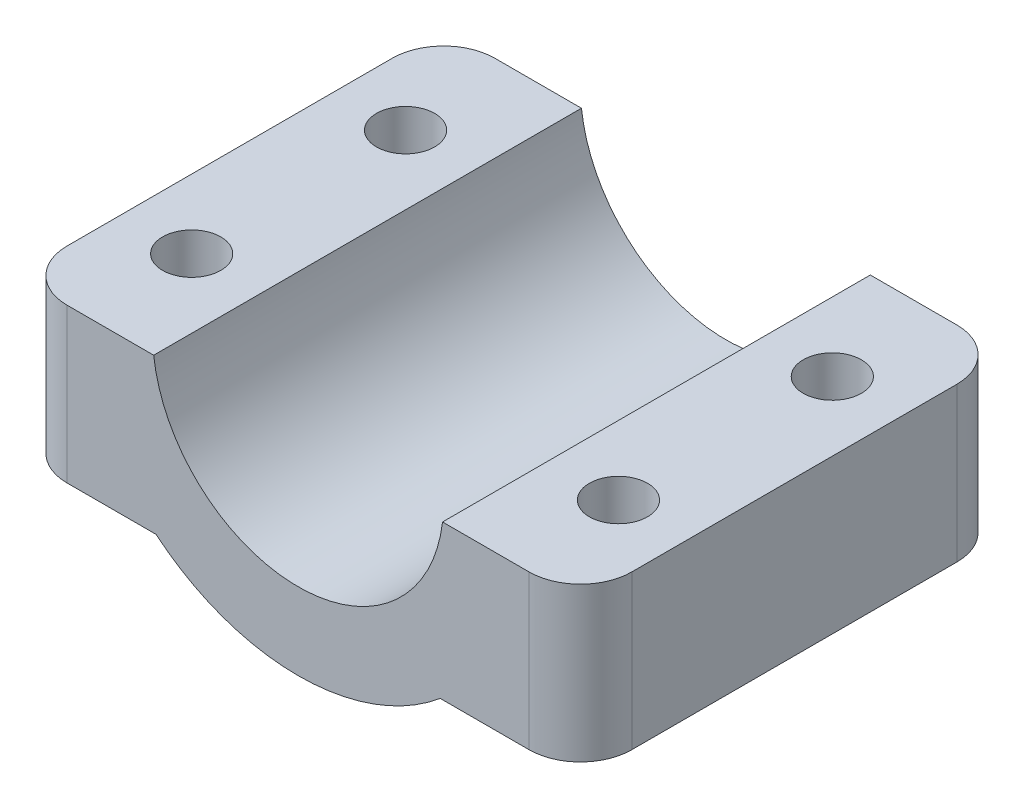
SolidWorks part; units mm, degrees
ref_plane "Alzado" through (0, 0, 0) normal (0, 0, 1) x (1, 0, 0)
ref_plane "Planta" through (0, 0, 0) normal (0, 1, 0) x (1, 0, 0)
ref_plane "Vista lateral" through (0, 0, 0) normal (1, 0, 0) x (0, 0, -1)
sketch "Croquis1" plane through (0, 0, 0) normal (0, 0, 1) x (1, 0, 0)
  line L0 (0, 0) -> (-17.9748, 0) construction
  line L1 (-16.5, 7.5) -> (-8.441, 7.5)
  line L2 (-16.5, 7.5) -> (-16.5, -1.5)
  line L5 (-16.5, 7.5) -> (16.5, -1.5) construction
  line L6 (-16.5, -1.5) -> (16.5, 7.5) construction
  line L15 (-16.5, -1.5) -> (-8.3066, -1.5)
  line L17 (8.441, 7.5) -> (16.5, 7.5)
  line L18 (8.3066, -1.5) -> (16.5, -1.5)
  line L19 (-12.4705, 7.5) -> (-12.4705, -1.5) construction
  line L20 (-14.1705, 7.5) -> (-14.1705, -1.5) construction
  line L21 (-10.7705, 7.5) -> (-10.7705, -1.5) construction
  line L22 (16.5, -1.5) -> (16.5, 7.5)
  arc A1 (-8.441, 7.5) -> (8.441, 7.5) centre (0, 8.5) ccw
  arc A7 (-8.3066, -1.5) -> (8.3066, -1.5) centre (0, 8.5) ccw
  point P0 (0, 0)
  point P7 (0, 0)
  dimension "D5" = 1
  dimension "D7" = 17
  dimension "D2" = 13
  dimension "D6" = 33
  dimension "D8" = 10
  dimension "D9" = 1.7
  dimension "D10" = 1.7
extrude "Saliente-Extruir1" add sketch "Croquis1" along normal mid plane 25
sketch "Croquis2" plane through (0, 7.5, 0) normal (0, 1, 0) x (1, 0, 0)
  line L0 (0, 12.5) -> (0, -12.5) construction
  line L1 (-8.441, -12.5) -> (8.441, -12.5) construction
  line L2 (8.441, 12.5) -> (-8.441, 12.5) construction
  line L3 (-16.5, 0) -> (16.5, 0) construction
  line L4 (-16.5, -12.5) -> (-16.5, 12.5) construction
  line L5 (16.5, -12.5) -> (16.5, 12.5) construction
  line L6 (-8.441, -12.5) -> (-16.5, -12.5) construction
  line L7 (-8.441, -12.5) -> (-16.5, -12.5) construction
  line L8 (-16.5, 0) -> (-16.5, 12.5) construction
  circle A2 centre (-12.4705, 6.25) radius 1.7
  circle A3 centre (12.4705, 6.25) radius 1.7
  circle A4 centre (12.4705, -6.25) radius 1.7
  circle A5 centre (-12.4705, -6.25) radius 1.7
  point P10 (-16.5, 6.25)
  point P13 (0, 12.5)
  point P24 (-12.4705, -12.5)
  dimension "D1" = 3.4
extrude "Cortar-Extruir1" cut sketch "Croquis2" against normal up to surface (9 mm away) contours A2
sketch "Croquis6" plane through (0, -1.5, 0) normal (0, -1, 0) x (1, 0, 0)
  line L0 (0, 6.25) -> (0, -6.25) construction
  line L1 (-12.4705, -6.25) -> (12.4705, -6.25) construction
  line L2 (-12.4705, -6.25) -> (-12.4705, 6.25) construction
  line L3 (-12.4705, 6.25) -> (12.4705, 6.25) construction
  line L4 (12.4705, -6.25) -> (12.4705, 6.25) construction
  line L5 (-12.4705, 0) -> (12.4705, 0) construction
  circle A0 centre (-12.4705, 6.25) radius 3.1
  circle A1 centre (12.4705, 6.25) radius 3.1
  circle A2 centre (12.4705, -6.25) radius 3.1
  circle A3 centre (-12.4705, -6.25) radius 3.1
  dimension "D1" = 6.2
extrude "Cortar-Extruir4" cut sketch "Croquis6" against normal blind 3
fillet "Redondeo1" radius 3 4 edges at (-16.5, 3, -12.5) (-16.5, 3, 12.5) (16.5, 3, -12.5) (16.5, 3, 12.5)
